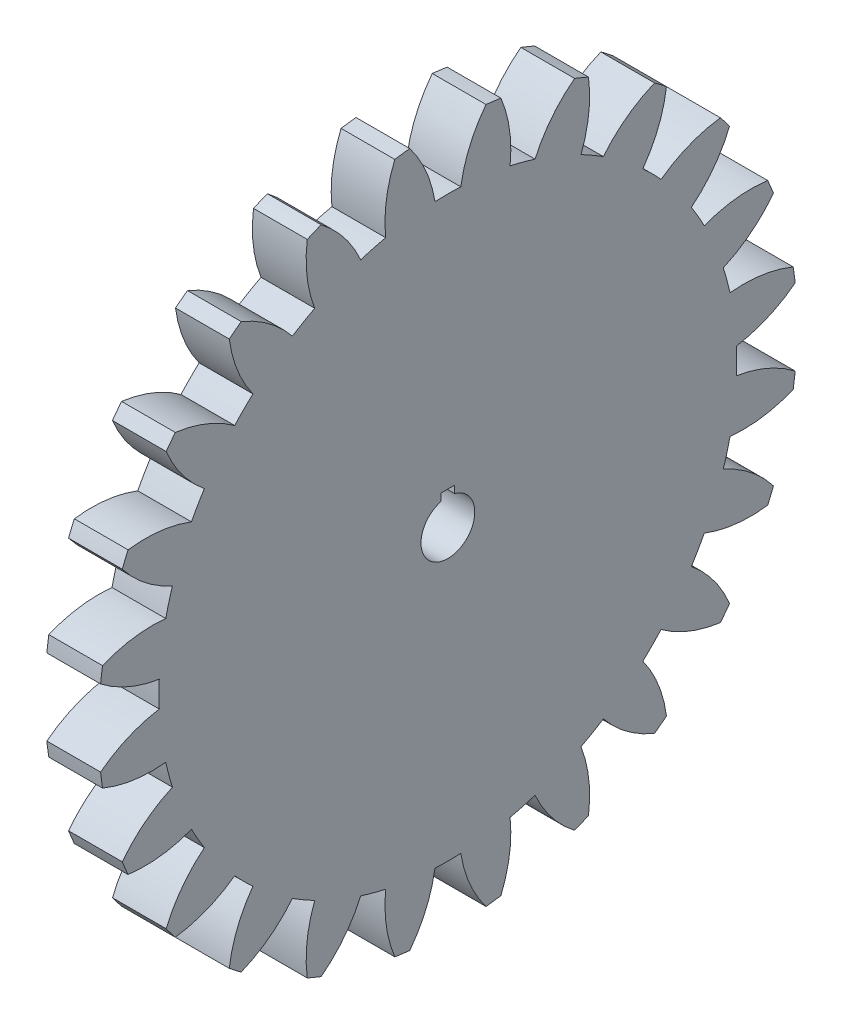
SolidWorks part; units mm, degrees
ref_plane "Plane1" through (0, 0, 0) normal (0, 0, 1) x (1, 0, 0)
ref_plane "Plane2" through (0, 0, 0) normal (0, 1, 0) x (1, 0, 0)
ref_plane "Plane3" through (0, 0, 0) normal (1, 0, 0) x (0, 0, -1)
sketch "HoldingSke" plane through (0, 0, 0) normal (0, 1, 0) x (1, 0, 0)
  line L0 (0, 0) -> (92.8162, -41.3244)
  line L1 (-15, 0) -> (100, 0) construction
  line L2 (0, 0) -> (-2.1039, 2.3779)
  line L3 (0, 0) -> (-11.863, 4.5341)
  line L4 (0, 0) -> (7.8894, 3.5126)
  line L5 (0, 0) -> (-47.5972, -17.7524)
  line L6 (0, 0) -> (-10.5278, -7.1032)
  line L7 (-2.1039, 2.3779) -> (8.8308, 51.9871)
  line L8 (-76.2, 54.61) -> (-61.976, 54.61)
  line L9 (-71.009, 38.7566) -> (-53.1078, 45.2721)
  line L10 (-76.2, 71.12) -> (104.1128, 71.12)
  line L11 (0, 0) -> (-12.7, 0)
  line L12 (-76.2, 101.6) -> (-75.9714, 101.6)
  line L13 (24.9733, 27.94) -> (52.9518, 28.4284)
  line L14 (24.9733, 27.94) -> (24.9746, 27.94)
  line L15 (24.9733, 27.94) -> (100.4006, 29.5858)
  circle A0 centre (0, 0) radius 6.35
  circle A1 centre (0, 0) radius 38.1
  circle A2 centre (0, 0) radius 38.1
  circle A3 centre (0, 0) radius 6.35
sketch "BasProSke" plane through (0, 0, 0) normal (0, 1, 0) x (1, 0, 0)
  line L0 (-10, 0) -> (60, 0) construction
  line L1 (0, 0) -> (0, 82.55)
  line L2 (0, 0) -> (12.7, 0)
  line L3 (12.7, 0) -> (12.7, 82.55)
  line L4 (12.7, 82.55) -> (0, 82.55)
revolve "Base-Revolve" add sketch "BasProSke" angle 360 about L0
sketch "TooCutSke" plane through (0, 0, 0) normal (1, 0, 0) x (0, 0, -1)
  line L1 (0, 0) -> (0, 107) construction
  line L2 (0, 0) -> (-5.3836, 76.0096) construction
  line L3 (0, 0) -> (-19.8562, 150.8226) construction
  line L4 (-5.3836, 76.0096) -> (-9.9281, 75.4113) construction
  arc A0 (3.0508, 68.193) -> (-3.0508, 68.193) centre (0, 0) ccw
  arc A1 (9.0282, 82.0804) -> (-9.0282, 82.0804) centre (0, 0) ccw
  circle A2 centre (0, 0) radius 76.2 construction
  circle A3 centre (0, 0) radius 71.6046 construction
  arc A4 (-3.0508, 68.193) -> (-9.0282, 82.0804) centre (-33.1615, 63.4628) ccw
  arc A5 (9.0282, 82.0804) -> (3.0508, 68.193) centre (33.1615, 63.4628) ccw
extrude "ToothCut" cut sketch "TooCutSke" along normal through all
fillet "Breaks" [suppressed] radius 0.127
fillet "RootFillets" [suppressed] radius 1.5888
pattern_circular "TeethCuts" count 24 every 15 about axis through (-10, 0, 0) along (1, 0, 0) of "ToothCut", "RootFillets", "Breaks"
sketch "HubNeaOneSke" plane through (0, 0, 0) normal (-1, 0, 0) x (0, 0, 1)
  circle A0 centre (0, 0) radius 38.1
extrude "HubNearOne" [suppressed] add sketch "HubNeaOneSke" along normal blind 38.1001
sketch "HubNeaBotSke" plane through (0, 0, 0) normal (-1, 0, 0) x (0, 0, 1)
  circle A0 centre (0, 0) radius 38.1
extrude "HubNearBoth" [suppressed] add sketch "HubNeaBotSke" along normal blind 19.05
ref_plane "FarPln" through (12.7, 0, 0) normal (1, 0, 0) x (0, 0, -1)
sketch "HubFarSke" plane through (12.7, 0, 0) normal (1, 0, 0) x (0, 0, -1)
  circle A0 centre (0, 0) radius 38.1
extrude "HubFar" [suppressed] add sketch "HubFarSke" along normal blind 19.05
sketch "BorSke" plane through (0, 0, 0) normal (1, 0, 0) x (0, 0, -1)
  circle A0 centre (0, 0) radius 6.35
extrude "Bore" cut sketch "BorSke" along normal mid plane 101.6001
sketch "KeySke" plane through (0, 0, 0) normal (1, 0, 0) x (0, 0, -1)
  line L0 (-1.5875, 0) -> (-1.5875, 7.874)
  line L1 (-1.5875, 7.874) -> (1.5875, 7.874)
  line L2 (1.5875, 7.874) -> (1.5875, 0)
  line L3 (0, 0) -> (0, 34) construction
  line L4 (-1.5875, 0) -> (1.5875, 0)
extrude "Keyway" cut sketch "KeySke" along normal mid plane 101.6001
pattern_circular "Keyway2" [suppressed] count 2 every 90 about axis through (-10, 0, 0) along (1, 0, 0)
equation "' \"Pitch@HoldingSke\" = 4"
equation "' \"Num_teeth@HoldingSke\" = 12"
equation "' \"Ap@HoldingSke\" =  20"
equation "' \"Ap@HoldingSke\" = 20"
equation "' \"Width@HoldingSke\" = 0.5"
equation "' \"Hub_dia@HoldingSke\"= 1"
equation "' \"Hub_dia@HoldingSke\" = 1"
equation "' \"Overall_len@HoldingSke\" = 1.0"
equation "' \"Bore@HoldingSke\" = 0.75"
equation "' \"T_dim@HoldingSke\" = 0.85"
equation "' \"Width@KeySke\" = 0.25"
equation "' \"Show_teeth@HoldingSke\" = 13"
equation "' \"Backlash@HoldingSke\" = 0.009"
equation "' \"Addendum_fac@HoldingSke\" = 1.0"
equation "' \"Dedendum_fac@HoldingSke\" = 1.25"
equation "' \"Dedendum_add@HoldingSke\" = 0.00005"
equation "' \"Clearance_fac@HoldingSke\" = 0.25"
equation "' \"Pitch@HoldingSke\" = 0.5"
equation "' \"Num_teeth@HoldingSke\" = 23"
equation "' \"Show_teeth@HoldingSke\" = 23"
equation "' \"Backlash@HoldingSke\" = 0.0375"
equation "\"Overcut_dia@TooCutSke\" = (\"Num_teeth@HoldingSke\" + 2 * \"Addendum_fac@HoldingSke\") / \"Pitch@HoldingSke\" + 0.002"
equation "\"Pitch_dia@TooCutSke\" = \"Num_teeth@HoldingSke\" / \"Pitch@HoldingSke\""
equation "\"Base_dia@TooCutSke\" = \"Num_teeth@HoldingSke\" / \"Pitch@HoldingSke\" * cos((\"Ap@HoldingSke\"  * 3.14159265 / 180))"
equation "\"Root_dia@TooCutSke\" = (\"Num_teeth@HoldingSke\" + 2) / \"Pitch@HoldingSke\" - 2 * (\"Addendum_fac@HoldingSke\" + \"Dedendum_fac@HoldingSke\") / \"Pitch@HoldingSke\" - \"Dedendum_add@HoldingSke\" * 2"
equation "\"Half_ang@TooCutSke\" = 180 / \"Num_teeth@HoldingSke\""
equation "\"Half_CT@TooCutSke\" = \"Num_teeth@HoldingSke\" / \"Pitch@HoldingSke\" * sin((3.14159265 / 2 / \"Num_teeth@HoldingSke\")) / 2 - 7 * \"Backlash@HoldingSke\" / 4"
equation "\"Flank_rad@TooCutSke\" = \"Num_teeth@HoldingSke\" / \"Pitch@HoldingSke\" / 5"
equation "\"Radius@RootFillets\" = \"Clearance_fac@HoldingSke\" / \"Pitch@HoldingSke\" + \"Dedendum_add@HoldingSke\""
equation "\"Break_rad@Breaks\" = 0.02 / \"Pitch@HoldingSke\""
equation "\"Thickness@HoldingSke\" = \"Width@HoldingSke\""
equation "\"OAL@HoldingSke\" = \"Thickness@HoldingSke\""
equation "\"MHD@HoldingSke\" = (\"Num_teeth@HoldingSke\" + 2) / \"Pitch@HoldingSke\" - 2 * (\"Addendum_fac@HoldingSke\" + \"Dedendum_fac@HoldingSke\")  / \"Pitch@HoldingSke\" - \"Dedendum_add@HoldingSke\" * 2"
equation "\"MBD@HoldingSke\" = (\"Num_teeth@HoldingSke\" + 2) / \"Pitch@HoldingSke\" - 2 * (\"Addendum_fac@HoldingSke\" + \"Dedendum_fac@HoldingSke\")  / \"Pitch@HoldingSke\" - \"Dedendum_add@HoldingSke\" * 2 - 0.002"
equation "\"MHD@HoldingSke\" = ((sgn( \"MHD@HoldingSke\" - \"Hub_dia@HoldingSke\" )-1)*( \"MHD@HoldingSke\" - \"Hub_dia@HoldingSke\" ))/-2+ \"Hub_dia@HoldingSke\""
equation "\"MBD@HoldingSke\" = ((sgn( \"MBD@HoldingSke\" - \"Bore@HoldingSke\" )-1)*( \"MBD@HoldingSke\" - \"Bore@HoldingSke\" ))/-2+ \"Bore@HoldingSke\""
equation "\"OAL@HoldingSke\" = ((sgn( \"OAL@HoldingSke\" - \"Overall_len@HoldingSke\" )+1)*( \"OAL@HoldingSke\" - \"Overall_len@HoldingSke\" ))/2 + \"Overall_len@HoldingSke\" + 0.000002"
equation "\"Num_teeth@TeethCuts\" = int( \"Show_teeth@HoldingSke\" ) + 1"
equation "\"Num_teeth@TeethCuts\" = ((sgn( \"Num_teeth@TeethCuts\" - \"Num_teeth@HoldingSke\" )-1)*( \"Num_teeth@TeethCuts\" - \"Num_teeth@HoldingSke\" ))/-2+ \"Num_teeth@HoldingSke\""
equation "\"Num_teeth@TeethCuts\" = ((sgn( \"Num_teeth@TeethCuts\" - 2.0)+1)*( \"Num_teeth@TeethCuts\" - 2.0))/2 +2.0"
equation "\"Angle@TeethCuts\" = 360.0 / \"Num_teeth@HoldingSke\""
equation "\"Diameter@BasProSke\" = (\"Num_teeth@HoldingSke\" + 2 * \"Addendum_fac@HoldingSke\") / \"Pitch@HoldingSke\""
equation "\"Thickness@BasProSke\"  = \"Thickness@HoldingSke\""
equation "' \"Fillet_rad@BasProSke\" =  \"Thickness@HoldingSke\" * 0.05"
equation "' \"Fillet_rad@BasProSke\" = \"Thickness@HoldingSke\" * 0.05"
equation "\"MHD@HoldingSke\" = ((sgn( \"MHD@HoldingSke\" - \"Root_dia@TooCutSke\" )-1)*( \"MHD@HoldingSke\" - \"Root_dia@TooCutSke\" ))/-2+ \"Root_dia@TooCutSke\""
equation "\"Diameter@HubNeaOneSke\" = \"MHD@HoldingSke\""
equation "\"Length@HubNearOne\" = \"OAL@HoldingSke\" - \"Thickness@BasProSke\""
equation "\"Diameter@HubNeaBotSke\" = \"MHD@HoldingSke\""
equation "\"Length@HubNearBoth\" = ( \"OAL@HoldingSke\" - \"Thickness@BasProSke\" ) / 2.0"
equation "\"Thickness@FarPln\" = \"Thickness@BasProSke\""
equation "\"Diameter@HubFarSke\" = \"MHD@HoldingSke\""
equation "\"Length@HubFar\" = ( \"OAL@HoldingSke\" - \"Thickness@BasProSke\" ) / 2.0"
equation "\"Diameter@BorSke\" = \"MBD@HoldingSke\""
equation "\"D1@Bore\" = \"OAL@HoldingSke\" * 2.0"
equation "\"D1@Keyway\" = \"OAL@HoldingSke\" * 2.0"
equation "\"Offset@KeySke\" = \"T_dim@HoldingSke\" - \"MBD@HoldingSke\" / 2.0"
